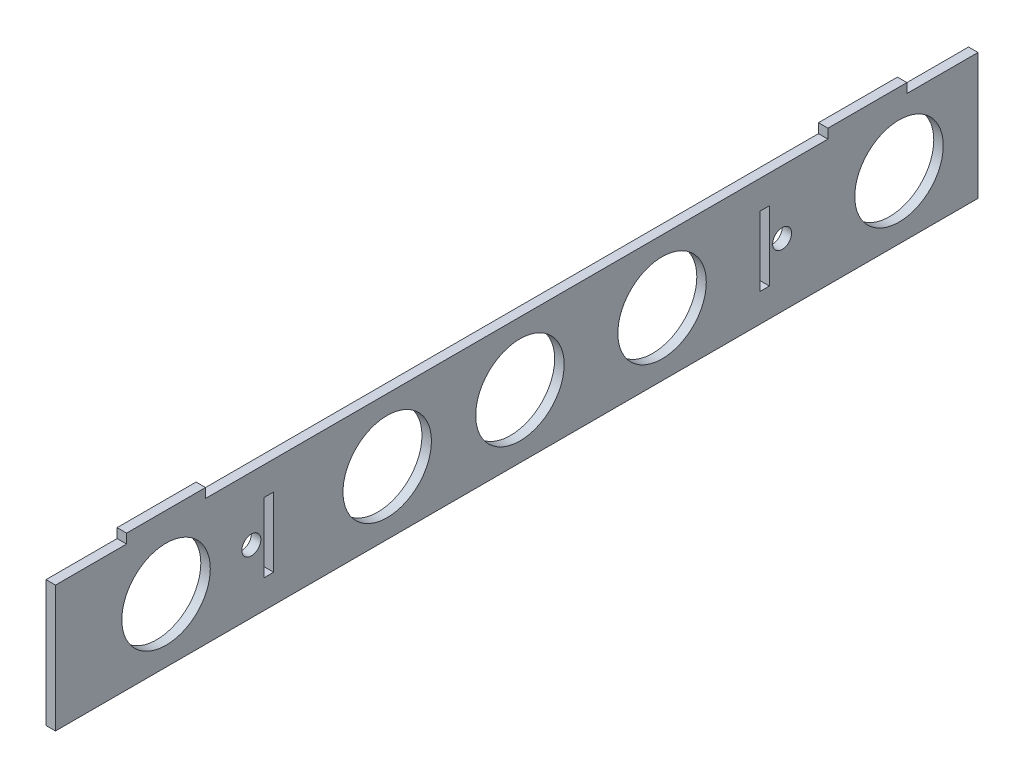
SolidWorks part; units mm, degrees
ref_plane "Front Plane" through (0, 0, 0) normal (0, 0, 1) x (1, 0, 0)
ref_plane "Top Plane" through (0, 0, 0) normal (0, 1, 0) x (1, 0, 0)
ref_plane "Right Plane" through (0, 0, 0) normal (1, 0, 0) x (0, 0, -1)
sketch "Sketch3" plane through (0, 0, 0) normal (1, 0, 0) x (0, 0, -1)
  line L1 (0, 0) -> (292, 0)
  line L2 (0, 0) -> (0, -40)
  line L3 (0, -40) -> (292, -40)
  line L4 (292, 0) -> (292, -40)
  line L5 (22.5, 0) -> (47.5, 0)
  line L6 (22.5, 0) -> (22.5, 3)
  line L7 (22.5, 3) -> (47.5, 3)
  line L8 (47.5, 0) -> (47.5, 3)
  line L9 (244.5, 0) -> (269.5, 0)
  line L10 (244.5, 0) -> (244.5, 3)
  line L11 (244.5, 3) -> (269.5, 3)
  line L12 (269.5, 0) -> (269.5, 3)
  line L13 (0, -9) -> (3, -9) construction
  line L14 (0, -9) -> (0, -31) construction
  line L15 (0, -31) -> (3, -31) construction
  line L16 (3, -9) -> (3, -31) construction
  line L17 (292, -9) -> (289, -9) construction
  line L18 (292, -9) -> (292, -31) construction
  line L19 (292, -31) -> (289, -31) construction
  line L20 (289, -9) -> (289, -31) construction
  line L21 (66.04, -9) -> (69.04, -9)
  line L22 (66.04, -9) -> (66.04, -31)
  line L23 (66.04, -31) -> (69.04, -31)
  line L24 (69.04, -9) -> (69.04, -31)
  line L25 (222.96, -9) -> (225.96, -9)
  line L26 (222.96, -9) -> (222.96, -31)
  line L27 (222.96, -31) -> (225.96, -31)
  line L28 (225.96, -9) -> (225.96, -31)
  point P29 (67.54, -9)
  point P30 (224.46, -9)
  point P32 (3, -20)
  point P33 (69.04, -20)
  point P34 (225.96, -20)
  point P35 (289, -20)
  point P36 (292, -20)
  point P37 (66.04, -20)
  point P38 (35, 3)
  point P39 (257, 3)
  dimension "D1" = 40
  dimension "D2" = 292
  dimension "D3" = 67.54
  dimension "D4" = 67.54
  dimension "D5" = 25
  dimension "D6" = 25
  dimension "D7" = 3
  dimension "D8" = 22
  dimension "D9" = 22
  dimension "D10" = 22
  dimension "D11" = 22
  dimension "D12" = 35
  dimension "D13" = 35
extrude "Boss-Extrude2" add sketch "Sketch3" along normal blind 3 contours L20 L17 L4 L1 L2 L13 L16 L15 L3 L19 L21 L24 L23 L22 L25 L28 L27 L26 | L1 L8 L7 L6 | L1 L12 L11 L10
sketch "Sketch5" plane through (3, 0, 0) normal (1, 0, 0) x (0, 0, -1)
  line L0 (0, -20) -> (292, -20) construction
  line L1 (0, 0) -> (0, -40) construction
  line L2 (292, 0) -> (292, -40) construction
  circle A0 centre (35, -20) radius 14
  circle A1 centre (105, -20) radius 14
  circle A2 centre (147, -20) radius 14
  circle A3 centre (192, -20) radius 14
  circle A4 centre (267, -20) radius 14
  point P16 (145.5512, -20)
  dimension "D1" = 28
  dimension "D2" = 35
  dimension "D3" = 105
  dimension "D4" = 100
  dimension "D5" = 25
  dimension "D6" = 147
extrude "Cut-Extrude1" cut sketch "Sketch5" against normal blind 10
sketch "Sketch6" plane through (3, 0, 0) normal (1, 0, 0) x (0, 0, -1)
  line L0 (0, -20) -> (292, -20) construction
  line L1 (0, 0) -> (0, -40) construction
  line L2 (292, 0) -> (292, -40) construction
  circle A0 centre (62, -20) radius 3
  circle A1 centre (230, -20) radius 3
  dimension "D1" = 6
  dimension "D4" = 6
  dimension "D2" = 62
  dimension "D3" = 62
extrude "Cut-Extrude2" cut sketch "Sketch6" against normal blind 10
